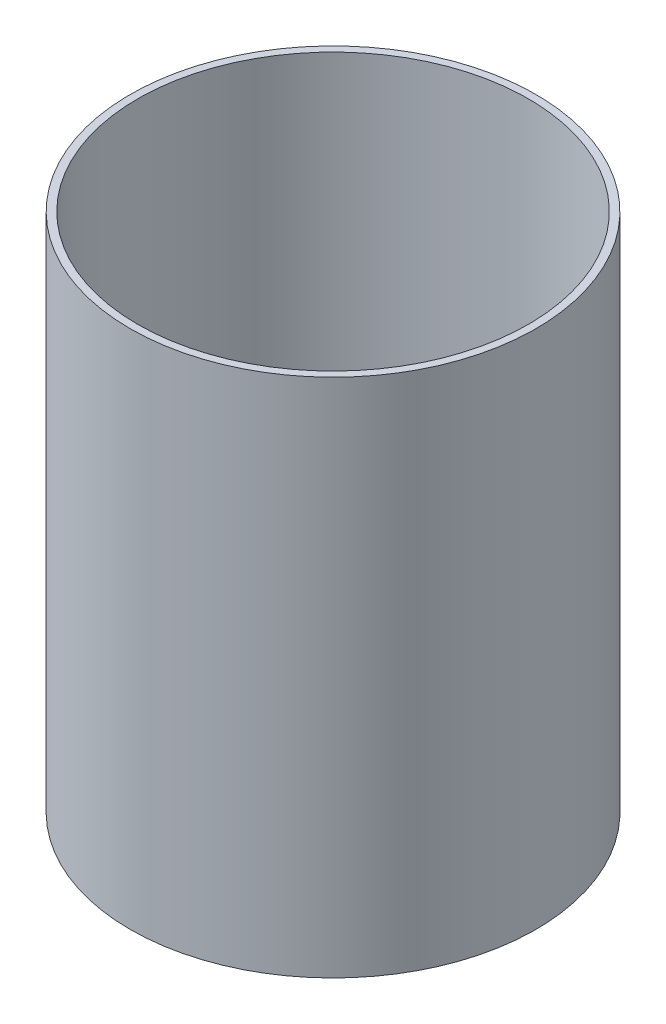
SolidWorks part; units mm, degrees
ref_plane "Front Plane" through (0, 0, 0) normal (0, 0, 1) x (1, 0, 0)
ref_plane "Top Plane" through (0, 0, 0) normal (0, 1, 0) x (1, 0, 0)
ref_plane "Right Plane" through (0, 0, 0) normal (1, 0, 0) x (0, 0, -1)
sketch "Sketch1" plane through (0, 0, 0) normal (0, 1, 0) x (1, 0, 0)
  circle A0 centre (0, 0) radius 49.5173
  circle A1 centre (0, 0) radius 47.6885
  dimension "D1" = 99.0346
  dimension "D2" = 95.377
extrude "Boss-Extrude1" add sketch "Sketch1" along normal blind 127
equation "\"Coupler_OD\" = 3.899in"
equation "\"Coupler_ID\" = 3.755in"
equation "\"Nosecone_Coupler_Length\" = 5in"
equation "\"D1@Sketch1\"=\"Coupler_OD\""
equation "\"D2@Sketch1\"=\"Coupler_ID\""
equation "\"D1@Boss-Extrude1\"=\"Nosecone_Coupler_Length\""
